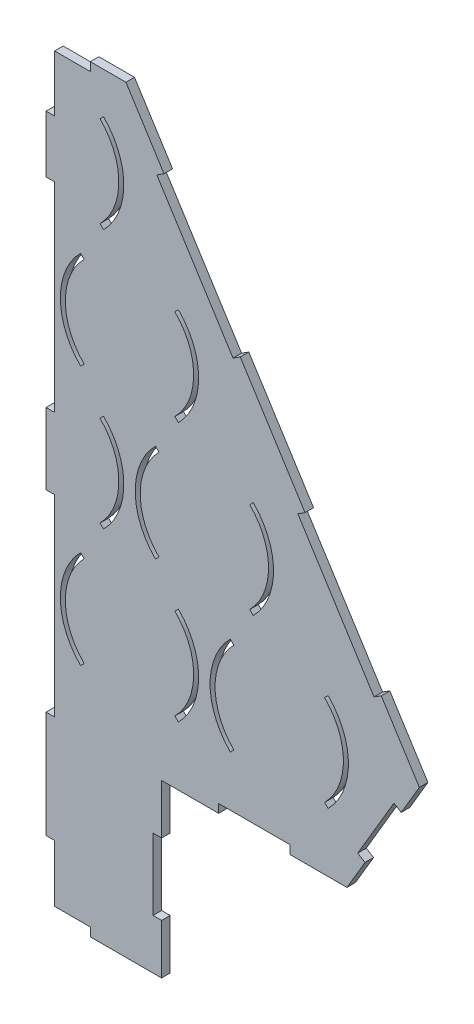
SolidWorks part; units mm, degrees
ref_plane "Plan de face" through (0, 0, 0) normal (0, 0, 1) x (1, 0, 0)
ref_plane "Plan de dessus" through (0, 0, 0) normal (0, 1, 0) x (1, 0, 0)
ref_plane "Plan de droite" through (0, 0, 0) normal (1, 0, 0) x (0, 0, -1)
sketch "Esquisse1" plane through (0, 0, 0) normal (0, 0, 1) x (1, 0, 0)
  line L0 (0, 0) -> (-371.1464, 0) construction
  line L1 (0, 0) -> (478.5179, 0) construction
  line L2 (0, 0) -> (0, 90.9327) construction
  line L3 (0, 90.9327) -> (-157.5, 90.9327) construction
  line L4 (0, 90.9327) -> (157.5, 90.9327) construction
  line L5 (0, 90.9327) -> (0, 181.8653) construction
  line L6 (0, 181.8653) -> (-52.5, 181.8653) construction
  line L7 (0, 181.8653) -> (52.5, 181.8653) construction
  line L8 (0, 181.8653) -> (0, 363.4062) construction
  line L12 (-157.5, 0) -> (-189.3198, -31.8198) construction
  line L13 (-157.5, 0) -> (-189.3198, 31.8198) construction
  line L14 (-189.3198, 31.8198) -> (-191.7947, 34.2947)
  line L15 (-189.3198, -31.8198) -> (-191.7947, -34.2947)
  line L16 (-157.5, 0) -> (-157.5, 43.1504) construction
  line L17 (-125.6802, 31.8198) -> (-123.2053, 34.2947)
  line L18 (-125.6802, -31.8198) -> (-123.2053, -34.2947)
  line L19 (-84.3198, -31.8198) -> (-86.7947, -34.2947)
  line L20 (-84.3198, 31.8198) -> (-86.7947, 34.2947)
  line L21 (-20.6802, 31.8198) -> (-18.2053, 34.2947)
  line L22 (-20.6802, -31.8198) -> (-18.2053, -34.2947)
  line L23 (20.6802, -31.8198) -> (18.2053, -34.2947)
  line L24 (20.6802, 31.8198) -> (18.2053, 34.2947)
  line L25 (84.3198, 31.8198) -> (86.7947, 34.2947)
  line L26 (84.3198, -31.8198) -> (86.7947, -34.2947)
  line L27 (125.6802, -31.8198) -> (123.2053, -34.2947)
  line L28 (125.6802, 31.8198) -> (123.2053, 34.2947)
  line L29 (189.3198, 31.8198) -> (191.7947, 34.2947)
  line L30 (189.3198, -31.8198) -> (191.7947, -34.2947)
  line L31 (-105, 90.9327) -> (-136.8198, 122.7525) construction
  line L32 (-105, 90.9327) -> (-136.8198, 59.1129) construction
  line L33 (-139.2947, 56.638) -> (-136.8198, 59.1129)
  line L34 (-136.8198, 122.7525) -> (-139.2947, 125.2273)
  line L35 (-105, 90.9327) -> (-105, 127.4436) construction
  line L36 (-70.7053, 56.638) -> (-73.1802, 59.1129)
  line L37 (-73.1802, 122.7525) -> (-70.7053, 125.2273)
  line L38 (-31.8198, 122.7525) -> (-34.2947, 125.2273)
  line L39 (-34.2947, 56.638) -> (-31.8198, 59.1129)
  line L40 (34.2947, 56.638) -> (31.8198, 59.1129)
  line L41 (31.8198, 122.7525) -> (34.2947, 125.2273)
  line L42 (73.1802, 122.7525) -> (70.7053, 125.2273)
  line L43 (70.7053, 56.638) -> (73.1802, 59.1129)
  line L44 (139.2947, 56.638) -> (136.8198, 59.1129)
  line L45 (136.8198, 122.7525) -> (139.2947, 125.2273)
  line L46 (-52.5, 181.8653) -> (-86.7947, 216.16) construction
  line L47 (-52.5, 181.8653) -> (-86.7947, 147.5707) construction
  line L48 (-52.5, 181.8653) -> (-100, 181.8653) construction
  line L49 (-84.3198, 213.6851) -> (-86.7947, 216.16)
  line L50 (-84.3198, 150.0455) -> (-86.7947, 147.5707)
  line L51 (-52.5, 181.8653) -> (-52.5, 219.5882) construction
  line L52 (-20.6802, 213.6851) -> (-18.2053, 216.16)
  line L53 (-20.6802, 150.0455) -> (-18.2053, 147.5707)
  line L54 (20.6802, 150.0455) -> (18.2053, 147.5707)
  line L55 (20.6802, 213.6851) -> (18.2053, 216.16)
  line L56 (84.3198, 150.0455) -> (86.7947, 147.5707)
  line L57 (84.3198, 213.6851) -> (86.7947, 216.16)
  line L58 (0, 272.798) -> (-34.2947, 307.0927) construction
  line L59 (0, 272.798) -> (-47.5, 272.798) construction
  line L60 (0, 272.798) -> (-34.2947, 238.5033) construction
  line L61 (-31.8198, 304.6178) -> (-34.2947, 307.0927)
  line L62 (-31.8198, 240.9782) -> (-34.2947, 238.5033)
  line L63 (31.8198, 304.6178) -> (34.2947, 307.0927)
  line L64 (31.8198, 240.9782) -> (34.2947, 238.5033)
  line L65 (-50, 335.9011) -> (50, 335.9011)
  line L66 (-255.7759, 10.5071) -> (-205, -75.6429)
  line L67 (255.7759, 10.5071) -> (205, -75.6429)
  line L68 (-205, -75.6429) -> (205, -75.6429)
  line L69 (-50, 335.9011) -> (-255.7759, 10.5071)
  line L70 (50, 335.9011) -> (255.7759, 10.5071)
  line L71 (-50, 335.9011) -> (-50, -75.6429) construction
  line L72 (50, 335.9011) -> (50, -75.6429) construction
  arc A10 (-189.3198, -31.8198) -> (-189.3198, 31.8198) centre (-157.5, 0) cw
  arc A11 (-191.7947, -34.2947) -> (-191.7947, 34.2947) centre (-157.5, 0) cw
  arc A12 (-125.6802, -31.8198) -> (-125.6802, 31.8198) centre (-157.5, 0) ccw
  arc A13 (-123.2053, -34.2947) -> (-123.2053, 34.2947) centre (-157.5, 0) ccw
  arc A14 (-86.7947, -34.2947) -> (-86.7947, 34.2947) centre (-52.5, 0) cw
  arc A15 (-84.3198, -31.8198) -> (-84.3198, 31.8198) centre (-52.5, 0) cw
  arc A16 (-20.6802, -31.8198) -> (-20.6802, 31.8198) centre (-52.5, 0) ccw
  arc A17 (-18.2053, -34.2947) -> (-18.2053, 34.2947) centre (-52.5, 0) ccw
  arc A18 (18.2053, -34.2947) -> (18.2053, 34.2947) centre (52.5, 0) cw
  arc A19 (20.6802, -31.8198) -> (20.6802, 31.8198) centre (52.5, 0) cw
  arc A20 (84.3198, -31.8198) -> (84.3198, 31.8198) centre (52.5, 0) ccw
  arc A21 (86.7947, -34.2947) -> (86.7947, 34.2947) centre (52.5, 0) ccw
  arc A22 (123.2053, -34.2947) -> (123.2053, 34.2947) centre (157.5, 0) cw
  arc A23 (125.6802, -31.8198) -> (125.6802, 31.8198) centre (157.5, 0) cw
  arc A24 (189.3198, -31.8198) -> (189.3198, 31.8198) centre (157.5, 0) ccw
  arc A25 (191.7947, -34.2947) -> (191.7947, 34.2947) centre (157.5, 0) ccw
  arc A26 (-136.8198, 122.7525) -> (-136.8198, 59.1129) centre (-105, 90.9327) ccw
  arc A27 (-139.2947, 125.2273) -> (-139.2947, 56.638) centre (-105, 90.9327) ccw
  arc A28 (-73.1802, 122.7525) -> (-73.1802, 59.1129) centre (-105, 90.9327) cw
  arc A29 (-70.7053, 125.2273) -> (-70.7053, 56.638) centre (-105, 90.9327) cw
  arc A30 (-34.2947, 125.2273) -> (-34.2947, 56.638) centre (0, 90.9327) ccw
  arc A31 (-31.8198, 122.7525) -> (-31.8198, 59.1129) centre (0, 90.9327) ccw
  arc A32 (31.8198, 122.7525) -> (31.8198, 59.1129) centre (0, 90.9327) cw
  arc A33 (34.2947, 125.2273) -> (34.2947, 56.638) centre (0, 90.9327) cw
  arc A34 (70.7053, 125.2273) -> (70.7053, 56.638) centre (105, 90.9327) ccw
  arc A35 (73.1802, 122.7525) -> (73.1802, 59.1129) centre (105, 90.9327) ccw
  arc A36 (136.8198, 122.7525) -> (136.8198, 59.1129) centre (105, 90.9327) cw
  arc A37 (139.2947, 125.2273) -> (139.2947, 56.638) centre (105, 90.9327) cw
  arc A38 (-86.7947, 216.16) -> (-86.7947, 147.5707) centre (-52.5, 181.8653) ccw
  arc A39 (-84.3198, 213.6851) -> (-84.3198, 150.0455) centre (-52.5, 181.8653) ccw
  arc A40 (-20.6802, 213.6851) -> (-20.6802, 150.0455) centre (-52.5, 181.8653) cw
  arc A41 (-18.2053, 216.16) -> (-18.2053, 147.5707) centre (-52.5, 181.8653) cw
  arc A42 (18.2053, 216.16) -> (18.2053, 147.5707) centre (52.5, 181.8653) ccw
  arc A43 (20.6802, 213.6851) -> (20.6802, 150.0455) centre (52.5, 181.8653) ccw
  arc A44 (84.3198, 213.6851) -> (84.3198, 150.0455) centre (52.5, 181.8653) cw
  arc A45 (86.7947, 216.16) -> (86.7947, 147.5707) centre (52.5, 181.8653) cw
  arc A46 (-34.2947, 307.0927) -> (-34.2947, 238.5033) centre (0, 272.798) ccw
  arc A47 (-31.8198, 304.6178) -> (-31.8198, 240.9782) centre (0, 272.798) ccw
  arc A48 (31.8198, 304.6178) -> (31.8198, 240.9782) centre (0, 272.798) cw
  arc A49 (34.2947, 307.0927) -> (34.2947, 238.5033) centre (0, 272.798) cw
  point P7 (-105, 90.9327)
  point P32 (-157.5, 0)
  point P95 (0, 272.798)
  dimension "D4" = 4
  dimension "D5" = 45
  dimension "D6" = 45
  dimension "D7" = 45
  dimension "D8" = 48.5
  dimension "D9" = 3
  dimension "D10" = 45
  dimension "D11" = 45
  dimension "D12" = 45
  dimension "D13" = 48.5
  dimension "D14" = 45
  dimension "D15" = 2
  dimension "D16" = 45
  dimension "D17" = 45
  dimension "D18" = 48.5
  dimension "D19" = 45
  dimension "D20" = 100
  dimension "D21" = 410
  dimension "D27" = 45
  dimension "D30" = 48.5
  dimension "D22" = 385
  dimension "D23" = 385
  dimension "D24" = 32.309
  dimension "D25" = 32.309
  dimension "D26" = 205
  dimension "D28" = 45
  dimension "D29" = 45
  dimension "D31" = 100
  dimension "D32" = 100
extrude "Boss.-Extru.1" add sketch "Esquisse1" along normal blind 6
sketch "Esquisse2" plane through (0, 0, 6) normal (0, 0, 1) x (1, 0, 0)
  line L0 (-205, -75.6429) -> (205, -75.6429) construction
  line L1 (75, -75.6429) -> (-75, -75.6429)
  line L2 (75, -75.6429) -> (75, -195.6429)
  line L3 (75, -195.6429) -> (-75, -195.6429)
  line L4 (-75, -75.6429) -> (-75, -195.6429)
  dimension "D1" = 150
  dimension "D2" = 120
  dimension "D3" = 75
extrude "Boss.-Extru.2" add sketch "Esquisse2" against normal blind 6
sketch "Esquisse3" plane through (0, 0, 6) normal (0, 0, 1) x (1, 0, 0)
  line L0 (-75, -75.6429) -> (-75, -195.6429) construction
  line L1 (-75, -110.6429) -> (-69, -110.6429)
  line L2 (-75, -110.6429) -> (-75, -160.6429)
  line L3 (-75, -160.6429) -> (-69, -160.6429)
  line L4 (-69, -110.6429) -> (-69, -160.6429)
  line L5 (-75, -195.6429) -> (75, -195.6429) construction
  line L6 (-25, -195.6429) -> (25, -195.6429)
  line L7 (-25, -195.6429) -> (-25, -189.6429)
  line L8 (-25, -189.6429) -> (25, -189.6429)
  line L9 (25, -195.6429) -> (25, -189.6429)
  line L10 (75, -195.6429) -> (75, -75.6429) construction
  line L11 (75, -110.6429) -> (69, -110.6429)
  line L12 (75, -110.6429) -> (75, -160.6429)
  line L13 (75, -160.6429) -> (69, -160.6429)
  line L14 (69, -110.6429) -> (69, -160.6429)
  line L15 (-205, -75.6429) -> (-75, -75.6429) construction
  line L16 (75, -75.6429) -> (205, -75.6429) construction
  dimension "D1" = 50
  dimension "D2" = 50
  dimension "D3" = 50
  dimension "D4" = 6
  dimension "D5" = 6
  dimension "D6" = 6
  dimension "D7" = 35
  dimension "D8" = 35
  dimension "D9" = 50
extrude "Enlèv. mat.-Extru.1" cut sketch "Esquisse3" against normal blind 10
sketch "Esquisse4" plane through (0, 0, 6) normal (0, 0, 1) x (1, 0, 0)
  line L0 (-205, -75.6429) -> (-75, -75.6429) construction
  line L1 (-165, -75.6429) -> (-115, -75.6429)
  line L2 (-165, -75.6429) -> (-165, -69.6429)
  line L3 (-165, -69.6429) -> (-115, -69.6429)
  line L4 (-115, -75.6429) -> (-115, -69.6429)
  line L11 (-217.694, -54.1054) -> (-212.525, -51.0588)
  line L12 (-255.7759, 10.5071) -> (-205, -75.6429) construction
  line L13 (-212.525, -51.0588) -> (-237.9129, -7.9839)
  line L14 (-237.9129, -7.9839) -> (-243.0819, -11.0304)
  line L15 (-243.0819, -11.0304) -> (-217.694, -54.1054)
  line L16 (-229.0517, 52.766) -> (-223.9806, 49.5592)
  line L17 (-50, 335.9011) -> (-255.7759, 10.5071) construction
  line L18 (-223.9806, 49.5592) -> (-170.5324, 134.0771)
  line L19 (-170.5324, 134.0771) -> (-175.6034, 137.284)
  line L20 (-175.6034, 137.284) -> (-229.0517, 52.766)
  line L23 (-71.6531, 290.4353) -> (-76.7241, 293.6422)
  line L25 (-71.6531, 290.4353) -> (-125.1013, 205.9173)
  line L26 (-125.1013, 205.9173) -> (-130.1724, 209.1242)
  line L27 (-130.1724, 209.1242) -> (-76.7241, 293.6422)
  line L28 (50, 335.9011) -> (-50, 335.9011) construction
  line L29 (-25, 335.9011) -> (25, 335.9011)
  line L30 (-25, 335.9011) -> (-25, 329.9011)
  line L31 (-25, 329.9011) -> (25, 329.9011)
  line L32 (25, 335.9011) -> (25, 329.9011)
  line L33 (0, 335.9011) -> (0, -65.6429) construction
  line L34 (165, -69.6429) -> (115, -69.6429)
  line L35 (115, -75.6429) -> (115, -69.6429)
  line L36 (165, -75.6429) -> (115, -75.6429)
  line L37 (165, -75.6429) -> (165, -69.6429)
  line L38 (237.9129, -7.9839) -> (243.0819, -11.0304)
  line L39 (212.525, -51.0588) -> (237.9129, -7.9839)
  line L40 (217.694, -54.1054) -> (212.525, -51.0588)
  line L41 (243.0819, -11.0304) -> (217.694, -54.1054)
  line L42 (170.5324, 134.0771) -> (175.6034, 137.284)
  line L43 (223.9806, 49.5592) -> (170.5324, 134.0771)
  line L44 (229.0517, 52.766) -> (223.9806, 49.5592)
  line L45 (175.6034, 137.284) -> (229.0517, 52.766)
  line L46 (125.1013, 205.9173) -> (130.1724, 209.1242)
  line L47 (71.6531, 290.4353) -> (125.1013, 205.9173)
  line L48 (71.6531, 290.4353) -> (76.7241, 293.6422)
  line L49 (130.1724, 209.1242) -> (76.7241, 293.6422)
  dimension "D1" = 6
  dimension "D2" = 50
  dimension "D3" = 6
  dimension "D4" = 50
  dimension "D5" = 40
  dimension "D6" = 25
  dimension "D7" = 6
  dimension "D8" = 100
  dimension "D9" = 6
  dimension "D10" = 50
  dimension "D11" = 50
  dimension "D12" = 100
  dimension "D13" = 6
  dimension "D14" = 50
  dimension "D15" = 25
extrude "Enlèv. mat.-Extru.2" cut sketch "Esquisse4" against normal blind 10
sketch "Esquisse7" plane through (0, 0, 6) normal (0, 0, 1) x (1, 0, 0)
  line L1 (0, 369.0955) -> (-293.707, 369.0955)
  line L2 (0, 369.0955) -> (0, -207.2011)
  line L3 (0, -207.2011) -> (-293.707, -207.2011)
  line L4 (-293.707, 369.0955) -> (-293.707, -207.2011)
extrude "Enlèv. mat.-Extru.4" cut sketch "Esquisse7" against normal blind 10
sketch "Esquisse8" plane through (0, 0, 6) normal (0, 0, 1) x (1, 0, 0)
  line L0 (0, -189.6429) -> (0, 329.9011) construction
  line L1 (0, 290.3571) -> (-6, 290.3571)
  line L2 (0, 290.3571) -> (0, 250.3571)
  line L3 (0, 250.3571) -> (-6, 250.3571)
  line L4 (-6, 290.3571) -> (-6, 250.3571)
  line L5 (25, -189.6429) -> (0, -189.6429) construction
  line L6 (0, 110.3571) -> (-6, 110.3571)
  line L7 (0, 110.3571) -> (0, 60.3571)
  line L8 (0, 60.3571) -> (-6, 60.3571)
  line L9 (-6, 110.3571) -> (-6, 60.3571)
  line L10 (0, -74.6429) -> (-6, -74.6429)
  line L11 (0, -74.6429) -> (0, -149.6429)
  line L12 (0, -149.6429) -> (-6, -149.6429)
  line L13 (-6, -74.6429) -> (-6, -149.6429)
  dimension "D1" = 75
  dimension "D2" = 50
  dimension "D3" = 40
  dimension "D4" = 6
  dimension "D5" = 6
  dimension "D6" = 6
  dimension "D7" = 40
  dimension "D8" = 135
  dimension "D9" = 140
extrude "Boss.-Extru.4" add sketch "Esquisse8" against normal blind 6
